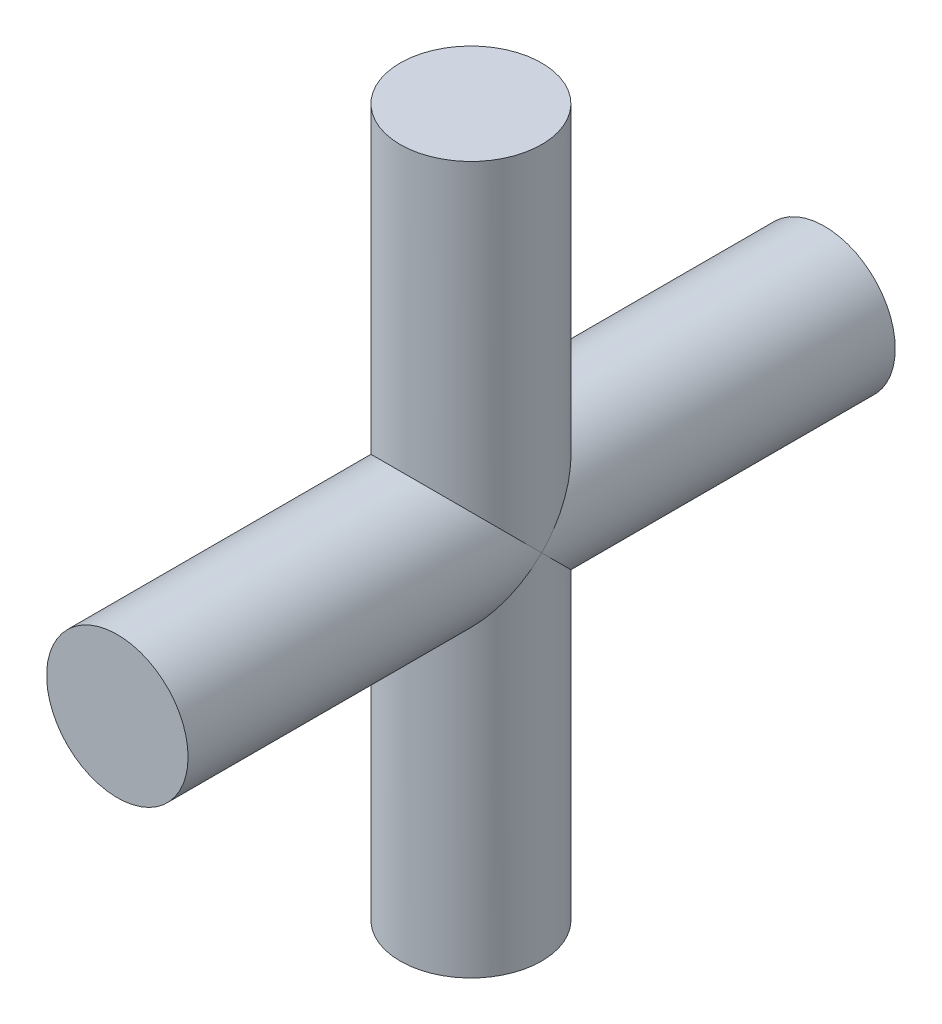
SolidWorks part; units mm, degrees
ref_plane "Front Plane" through (0, 0, 0) normal (0, 0, 1) x (1, 0, 0)
ref_plane "Top Plane" through (0, 0, 0) normal (0, 1, 0) x (1, 0, 0)
ref_plane "Right Plane" through (0, 0, 0) normal (1, 0, 0) x (0, 0, -1)
sketch "Sketch2" plane through (0, 0, 0) normal (0, 0, 1) x (1, 0, 0)
  circle A0 centre (0, 0) radius 5
  dimension "D1" = 10
extrude "Boss-Extrude1" add sketch "Sketch2" along normal blind 50
ref_plane "Plane1" through (0, 25, 0) normal (0, 1, 0) x (1, 0, 0)
sketch "Sketch5" plane through (0, 25, 0) normal (0, 1, 0) x (1, 0, 0)
  circle A0 centre (0, -25) radius 5
  point P2 (0, 0)
  point P4 (0, 0)
  point P5 (0, 0)
  dimension "D1" = 10
  dimension "D2" = 25
extrude "Boss-Extrude2" add sketch "Sketch5" against normal blind 50
